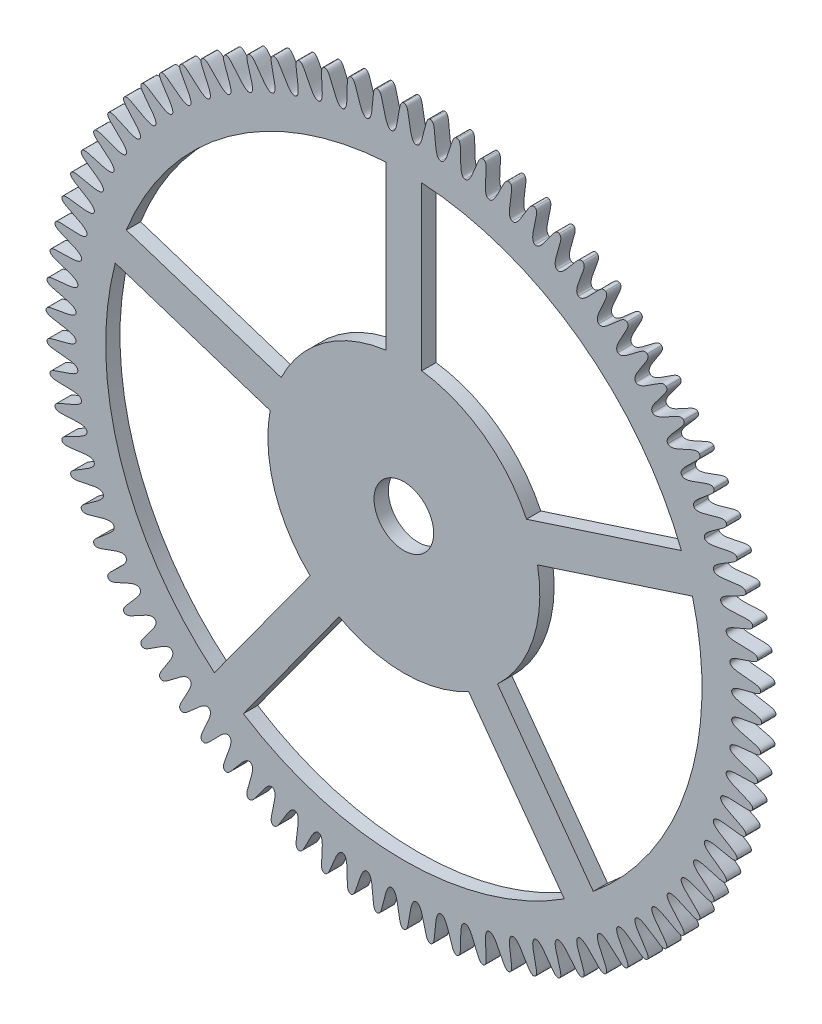
SolidWorks part; units mm, degrees
ref_plane "Alzado" through (0, 0, 0) normal (0, 0, 1) x (1, 0, 0)
ref_plane "Planta" through (0, 0, 0) normal (0, 1, 0) x (1, 0, 0)
ref_plane "Vista lateral" through (0, 0, 0) normal (1, 0, 0) x (0, 0, -1)
sketch "Sketch1" plane through (0, 0, 0) normal (0, 0, 1) x (1, 0, 0)
  line L0 (0, -5096.8663) -> (0, 249746.4475) construction
  line L1 (-5096.8663, 0) -> (249746.4475, 0) construction
  line L2 (0, 0) -> (1869.5597, 49965.0352) construction
  line L3 (0, 0) -> (-1869.5597, 49965.0352) construction
  circle A0 centre (0, 0) radius 6 construction
  circle A1 centre (0, 0) radius 5.5 construction
  circle A2 centre (0, 0) radius 5.75 construction
  spline S0 degree 3 poles (0, 6) (0.0624, 5.9999) (0.0733, 5.8707) (0.1163, 5.6176) (0.1469, 5.4976) (0.2057, 5.4979) knots 0 0 0 0 0.435079 0.535079 1 1 1 1
  spline S1 degree 3 poles (0, 6) (-0.0624, 5.9999) (-0.0733, 5.8707) (-0.1163, 5.6176) (-0.1469, 5.4976) (-0.2057, 5.4979) knots 0 0 0 0 0.435079 0.535079 1 1 1 1
  spline S2 degree 3 poles (0.4484, 5.9832) (0.3861, 5.9878) (0.3657, 5.8598) (0.3038, 5.6106) (0.2644, 5.4932) (0.2057, 5.4979) knots 0 0 0 0 0.435079 0.535079 1 1 1 1
  spline S3 degree 3 poles (0.4484, 5.9832) (0.5106, 5.9785) (0.5118, 5.8488) (0.5358, 5.5932) (0.5573, 5.4712) (0.616, 5.4672) knots 0 0 0 0 0.435079 0.535079 1 1 1 1
  spline S4 degree 3 poles (0.8943, 5.933) (0.8325, 5.9422) (0.8026, 5.8161) (0.7223, 5.5722) (0.6741, 5.4581) (0.616, 5.4672) knots 0 0 0 0 0.435079 0.535079 1 1 1 1
  spline S5 degree 3 poles (0.8943, 5.933) (0.956, 5.9236) (0.9474, 5.7942) (0.9522, 5.5375) (0.9646, 5.4143) (1.0228, 5.4059) knots 0 0 0 0 0.435079 0.535079 1 1 1 1
  spline S6 degree 3 poles (1.3351, 5.8496) (1.2743, 5.8634) (1.2349, 5.7398) (1.1367, 5.5026) (1.0801, 5.3924) (1.0228, 5.4059) knots 0 0 0 0 0.435079 0.535079 1 1 1 1
  spline S7 degree 3 poles (1.3351, 5.8496) (1.396, 5.8356) (1.3778, 5.7072) (1.3634, 5.4509) (1.3665, 5.3271) (1.424, 5.3143) knots 0 0 0 0 0.435079 0.535079 1 1 1 1
  spline S8 degree 3 poles (1.7685, 5.7334) (1.7089, 5.7518) (1.6604, 5.6315) (1.5447, 5.4023) (1.4801, 5.2966) (1.424, 5.3143) knots 0 0 0 0 0.435079 0.535079 1 1 1 1
  spline S9 degree 3 poles (1.7685, 5.7334) (1.8281, 5.715) (1.8004, 5.5883) (1.7669, 5.3337) (1.7608, 5.21) (1.8171, 5.193) knots 0 0 0 0 0.435079 0.535079 1 1 1 1
  spline S10 degree 3 poles (2.192, 5.5852) (2.1339, 5.608) (2.0766, 5.4917) (1.9441, 5.2717) (1.8718, 5.1712) (1.8171, 5.193) knots 0 0 0 0 0.435079 0.535079 1 1 1 1
  spline S11 degree 3 poles (2.192, 5.5852) (2.2501, 5.5624) (2.213, 5.4381) (2.1606, 5.1868) (2.1452, 5.0639) (2.2001, 5.0427) knots 0 0 0 0 0.435079 0.535079 1 1 1 1
  spline S12 degree 3 poles (2.6033, 5.4058) (2.5471, 5.4328) (2.4812, 5.3211) (2.3326, 5.1117) (2.253, 5.0169) (2.2001, 5.0427) knots 0 0 0 0 0.435079 0.535079 1 1 1 1
  spline S13 degree 3 poles (2.6033, 5.4058) (2.6595, 5.3787) (2.6132, 5.2575) (2.5421, 5.0108) (2.5176, 4.8894) (2.5708, 4.8642) knots 0 0 0 0 0.435079 0.535079 1 1 1 1
  spline S14 degree 3 poles (3, 5.1962) (2.9459, 5.2273) (2.8719, 5.1208) (2.7081, 4.9231) (2.6216, 4.8345) (2.5708, 4.8642) knots 0 0 0 0 0.435079 0.535079 1 1 1 1
  spline S15 degree 3 poles (3, 5.1962) (3.054, 5.1649) (2.9988, 5.0476) (2.9095, 4.8068) (2.876, 4.6876) (2.9271, 4.6585) knots 0 0 0 0 0.435079 0.535079 1 1 1 1
  spline S16 degree 3 poles (3.3799, 4.9574) (3.3283, 4.9925) (3.2466, 4.8919) (3.0684, 4.707) (2.9755, 4.625) (2.9271, 4.6585) knots 0 0 0 0 0.435079 0.535079 1 1 1 1
  spline S17 degree 3 poles (3.3799, 4.9574) (3.4315, 4.9222) (3.3676, 4.8093) (3.2606, 4.576) (3.2182, 4.4596) (3.2671, 4.4267) knots 0 0 0 0 0.435079 0.535079 1 1 1 1
  spline S18 degree 3 poles (3.7409, 4.691) (3.6921, 4.7299) (3.6031, 4.6356) (3.4116, 4.4645) (3.3129, 4.3897) (3.2671, 4.4267) knots 0 0 0 0 0.435079 0.535079 1 1 1 1
  spline S19 degree 3 poles (3.7409, 4.691) (3.7897, 4.652) (3.7176, 4.5442) (3.5934, 4.3195) (3.5425, 4.2066) (3.5887, 4.1702) knots 0 0 0 0 0.435079 0.535079 1 1 1 1
  spline S20 degree 3 poles (4.081, 4.3983) (4.0353, 4.4407) (3.9394, 4.3534) (3.7357, 4.1971) (3.6316, 4.1299) (3.5887, 4.1702) knots 0 0 0 0 0.435079 0.535079 1 1 1 1
  spline S21 degree 3 poles (4.081, 4.3983) (4.1267, 4.3558) (4.0468, 4.2537) (3.9062, 4.0389) (3.847, 3.9301) (3.8904, 3.8904) knots 0 0 0 0 0.435079 0.535079 1 1 1 1
  spline S22 degree 3 poles (4.3983, 4.081) (4.3558, 4.1267) (4.2537, 4.0468) (4.0389, 3.9062) (3.9301, 3.847) (3.8904, 3.8904) knots 0 0 0 0 0.435079 0.535079 1 1 1 1
  spline S23 degree 3 poles (4.3983, 4.081) (4.4407, 4.0353) (4.3534, 3.9394) (4.1971, 3.7357) (4.1299, 3.6316) (4.1702, 3.5887) knots 0 0 0 0 0.435079 0.535079 1 1 1 1
  spline S24 degree 3 poles (4.691, 3.7409) (4.652, 3.7897) (4.5442, 3.7176) (4.3195, 3.5934) (4.2066, 3.5425) (4.1702, 3.5887) knots 0 0 0 0 0.435079 0.535079 1 1 1 1
  spline S25 degree 3 poles (4.691, 3.7409) (4.7299, 3.6921) (4.6356, 3.6031) (4.4645, 3.4116) (4.3897, 3.3129) (4.4267, 3.2671) knots 0 0 0 0 0.435079 0.535079 1 1 1 1
  spline S26 degree 3 poles (4.9574, 3.3799) (4.9222, 3.4315) (4.8093, 3.3676) (4.576, 3.2606) (4.4596, 3.2182) (4.4267, 3.2671) knots 0 0 0 0 0.435079 0.535079 1 1 1 1
  spline S27 degree 3 poles (4.9574, 3.3799) (4.9925, 3.3283) (4.8919, 3.2466) (4.707, 3.0684) (4.625, 2.9755) (4.6585, 2.9271) knots 0 0 0 0 0.435079 0.535079 1 1 1 1
  spline S28 degree 3 poles (5.1962, 3) (5.1649, 3.054) (5.0476, 2.9988) (4.8068, 2.9095) (4.6876, 2.876) (4.6585, 2.9271) knots 0 0 0 0 0.435079 0.535079 1 1 1 1
  spline S29 degree 3 poles (5.1962, 3) (5.2273, 2.9459) (5.1208, 2.8719) (4.9231, 2.7081) (4.8345, 2.6216) (4.8642, 2.5708) knots 0 0 0 0 0.435079 0.535079 1 1 1 1
  spline S30 degree 3 poles (5.4058, 2.6033) (5.3787, 2.6595) (5.2575, 2.6132) (5.0108, 2.5421) (4.8894, 2.5176) (4.8642, 2.5708) knots 0 0 0 0 0.435079 0.535079 1 1 1 1
  spline S31 degree 3 poles (5.4058, 2.6033) (5.4328, 2.5471) (5.3211, 2.4812) (5.1117, 2.3326) (5.0169, 2.253) (5.0427, 2.2001) knots 0 0 0 0 0.435079 0.535079 1 1 1 1
  spline S32 degree 3 poles (5.5852, 2.192) (5.5624, 2.2501) (5.4381, 2.213) (5.1868, 2.1606) (5.0639, 2.1452) (5.0427, 2.2001) knots 0 0 0 0 0.435079 0.535079 1 1 1 1
  spline S33 degree 3 poles (5.5852, 2.192) (5.608, 2.1339) (5.4917, 2.0766) (5.2717, 1.9441) (5.1712, 1.8718) (5.193, 1.8171) knots 0 0 0 0 0.435079 0.535079 1 1 1 1
  spline S34 degree 3 poles (5.7334, 1.7685) (5.715, 1.8281) (5.5883, 1.8004) (5.3337, 1.7669) (5.21, 1.7608) (5.193, 1.8171) knots 0 0 0 0 0.435079 0.535079 1 1 1 1
  spline S35 degree 3 poles (5.7334, 1.7685) (5.7518, 1.7089) (5.6315, 1.6604) (5.4023, 1.5447) (5.2966, 1.4801) (5.3143, 1.424) knots 0 0 0 0 0.435079 0.535079 1 1 1 1
  spline S36 degree 3 poles (5.8496, 1.3351) (5.8356, 1.396) (5.7072, 1.3778) (5.4509, 1.3634) (5.3271, 1.3665) (5.3143, 1.424) knots 0 0 0 0 0.435079 0.535079 1 1 1 1
  spline S37 degree 3 poles (5.8496, 1.3351) (5.8634, 1.2743) (5.7398, 1.2349) (5.5026, 1.1367) (5.3924, 1.0801) (5.4059, 1.0228) knots 0 0 0 0 0.435079 0.535079 1 1 1 1
  spline S38 degree 3 poles (5.933, 0.8943) (5.9236, 0.956) (5.7942, 0.9474) (5.5375, 0.9522) (5.4143, 0.9646) (5.4059, 1.0228) knots 0 0 0 0 0.435079 0.535079 1 1 1 1
  spline S39 degree 3 poles (5.933, 0.8943) (5.9422, 0.8325) (5.8161, 0.8026) (5.5722, 0.7223) (5.4581, 0.6741) (5.4672, 0.616) knots 0 0 0 0 0.435079 0.535079 1 1 1 1
  spline S40 degree 3 poles (5.9832, 0.4484) (5.9785, 0.5106) (5.8488, 0.5118) (5.5932, 0.5358) (5.4712, 0.5573) (5.4672, 0.616) knots 0 0 0 0 0.435079 0.535079 1 1 1 1
  spline S41 degree 3 poles (5.9832, 0.4484) (5.9878, 0.3861) (5.8598, 0.3657) (5.6106, 0.3038) (5.4932, 0.2644) (5.4979, 0.2057) knots 0 0 0 0 0.435079 0.535079 1 1 1 1
  spline S42 degree 3 poles (6, 0) (5.9999, 0.0624) (5.8707, 0.0733) (5.6176, 0.1163) (5.4976, 0.1469) (5.4979, 0.2057) knots 0 0 0 0 0.435079 0.535079 1 1 1 1
  spline S43 degree 3 poles (6, 0) (5.9999, -0.0624) (5.8707, -0.0733) (5.6176, -0.1163) (5.4976, -0.1469) (5.4979, -0.2057) knots 0 0 0 0 0.435079 0.535079 1 1 1 1
  spline S44 degree 3 poles (5.9832, -0.4484) (5.9878, -0.3861) (5.8598, -0.3657) (5.6106, -0.3038) (5.4932, -0.2644) (5.4979, -0.2057) knots 0 0 0 0 0.435079 0.535079 1 1 1 1
  spline S45 degree 3 poles (5.9832, -0.4484) (5.9785, -0.5106) (5.8488, -0.5118) (5.5932, -0.5358) (5.4712, -0.5573) (5.4672, -0.616) knots 0 0 0 0 0.435079 0.535079 1 1 1 1
  spline S46 degree 3 poles (5.933, -0.8943) (5.9422, -0.8325) (5.8161, -0.8026) (5.5722, -0.7223) (5.4581, -0.6741) (5.4672, -0.616) knots 0 0 0 0 0.435079 0.535079 1 1 1 1
  spline S47 degree 3 poles (5.933, -0.8943) (5.9236, -0.956) (5.7942, -0.9474) (5.5375, -0.9522) (5.4143, -0.9646) (5.4059, -1.0228) knots 0 0 0 0 0.435079 0.535079 1 1 1 1
  spline S48 degree 3 poles (5.8496, -1.3351) (5.8634, -1.2743) (5.7398, -1.2349) (5.5026, -1.1367) (5.3924, -1.0801) (5.4059, -1.0228) knots 0 0 0 0 0.435079 0.535079 1 1 1 1
  spline S49 degree 3 poles (5.8496, -1.3351) (5.8356, -1.396) (5.7072, -1.3778) (5.4509, -1.3634) (5.3271, -1.3665) (5.3143, -1.424) knots 0 0 0 0 0.435079 0.535079 1 1 1 1
  spline S50 degree 3 poles (5.7334, -1.7685) (5.7518, -1.7089) (5.6315, -1.6604) (5.4023, -1.5447) (5.2966, -1.4801) (5.3143, -1.424) knots 0 0 0 0 0.435079 0.535079 1 1 1 1
  spline S51 degree 3 poles (5.7334, -1.7685) (5.715, -1.8281) (5.5883, -1.8004) (5.3337, -1.7669) (5.21, -1.7608) (5.193, -1.8171) knots 0 0 0 0 0.435079 0.535079 1 1 1 1
  spline S52 degree 3 poles (5.5852, -2.192) (5.608, -2.1339) (5.4917, -2.0766) (5.2717, -1.9441) (5.1712, -1.8718) (5.193, -1.8171) knots 0 0 0 0 0.435079 0.535079 1 1 1 1
  spline S53 degree 3 poles (5.5852, -2.192) (5.5624, -2.2501) (5.4381, -2.213) (5.1868, -2.1606) (5.0639, -2.1452) (5.0427, -2.2001) knots 0 0 0 0 0.435079 0.535079 1 1 1 1
  spline S54 degree 3 poles (5.4058, -2.6033) (5.4328, -2.5471) (5.3211, -2.4812) (5.1117, -2.3326) (5.0169, -2.253) (5.0427, -2.2001) knots 0 0 0 0 0.435079 0.535079 1 1 1 1
  spline S55 degree 3 poles (5.4058, -2.6033) (5.3787, -2.6595) (5.2575, -2.6132) (5.0108, -2.5421) (4.8894, -2.5176) (4.8642, -2.5708) knots 0 0 0 0 0.435079 0.535079 1 1 1 1
  spline S56 degree 3 poles (5.1962, -3) (5.2273, -2.9459) (5.1208, -2.8719) (4.9231, -2.7081) (4.8345, -2.6216) (4.8642, -2.5708) knots 0 0 0 0 0.435079 0.535079 1 1 1 1
  spline S57 degree 3 poles (5.1962, -3) (5.1649, -3.054) (5.0476, -2.9988) (4.8068, -2.9095) (4.6876, -2.876) (4.6585, -2.9271) knots 0 0 0 0 0.435079 0.535079 1 1 1 1
  spline S58 degree 3 poles (4.9574, -3.3799) (4.9925, -3.3283) (4.8919, -3.2466) (4.707, -3.0684) (4.625, -2.9755) (4.6585, -2.9271) knots 0 0 0 0 0.435079 0.535079 1 1 1 1
  spline S59 degree 3 poles (4.9574, -3.3799) (4.9222, -3.4315) (4.8093, -3.3676) (4.576, -3.2606) (4.4596, -3.2182) (4.4267, -3.2671) knots 0 0 0 0 0.435079 0.535079 1 1 1 1
  spline S60 degree 3 poles (4.691, -3.7409) (4.7299, -3.6921) (4.6356, -3.6031) (4.4645, -3.4116) (4.3897, -3.3129) (4.4267, -3.2671) knots 0 0 0 0 0.435079 0.535079 1 1 1 1
  spline S61 degree 3 poles (4.691, -3.7409) (4.652, -3.7897) (4.5442, -3.7176) (4.3195, -3.5934) (4.2066, -3.5425) (4.1702, -3.5887) knots 0 0 0 0 0.435079 0.535079 1 1 1 1
  spline S62 degree 3 poles (4.3983, -4.081) (4.4407, -4.0353) (4.3534, -3.9394) (4.1971, -3.7357) (4.1299, -3.6316) (4.1702, -3.5887) knots 0 0 0 0 0.435079 0.535079 1 1 1 1
  spline S63 degree 3 poles (4.3983, -4.081) (4.3558, -4.1267) (4.2537, -4.0468) (4.0389, -3.9062) (3.9301, -3.847) (3.8904, -3.8904) knots 0 0 0 0 0.435079 0.535079 1 1 1 1
  spline S64 degree 3 poles (4.081, -4.3983) (4.1267, -4.3558) (4.0468, -4.2537) (3.9062, -4.0389) (3.847, -3.9301) (3.8904, -3.8904) knots 0 0 0 0 0.435079 0.535079 1 1 1 1
  spline S65 degree 3 poles (4.081, -4.3983) (4.0353, -4.4407) (3.9394, -4.3534) (3.7357, -4.1971) (3.6316, -4.1299) (3.5887, -4.1702) knots 0 0 0 0 0.435079 0.535079 1 1 1 1
  spline S66 degree 3 poles (3.7409, -4.691) (3.7897, -4.652) (3.7176, -4.5442) (3.5934, -4.3195) (3.5425, -4.2066) (3.5887, -4.1702) knots 0 0 0 0 0.435079 0.535079 1 1 1 1
  spline S67 degree 3 poles (3.7409, -4.691) (3.6921, -4.7299) (3.6031, -4.6356) (3.4116, -4.4645) (3.3129, -4.3897) (3.2671, -4.4267) knots 0 0 0 0 0.435079 0.535079 1 1 1 1
  spline S68 degree 3 poles (3.3799, -4.9574) (3.4315, -4.9222) (3.3676, -4.8093) (3.2606, -4.576) (3.2182, -4.4596) (3.2671, -4.4267) knots 0 0 0 0 0.435079 0.535079 1 1 1 1
  spline S69 degree 3 poles (3.3799, -4.9574) (3.3283, -4.9925) (3.2466, -4.8919) (3.0684, -4.707) (2.9755, -4.625) (2.9271, -4.6585) knots 0 0 0 0 0.435079 0.535079 1 1 1 1
  spline S70 degree 3 poles (3, -5.1962) (3.054, -5.1649) (2.9988, -5.0476) (2.9095, -4.8068) (2.876, -4.6876) (2.9271, -4.6585) knots 0 0 0 0 0.435079 0.535079 1 1 1 1
  spline S71 degree 3 poles (3, -5.1962) (2.9459, -5.2273) (2.8719, -5.1208) (2.7081, -4.9231) (2.6216, -4.8345) (2.5708, -4.8642) knots 0 0 0 0 0.435079 0.535079 1 1 1 1
  spline S72 degree 3 poles (2.6033, -5.4058) (2.6595, -5.3787) (2.6132, -5.2575) (2.5421, -5.0108) (2.5176, -4.8894) (2.5708, -4.8642) knots 0 0 0 0 0.435079 0.535079 1 1 1 1
  spline S73 degree 3 poles (2.6033, -5.4058) (2.5471, -5.4328) (2.4812, -5.3211) (2.3326, -5.1117) (2.253, -5.0169) (2.2001, -5.0427) knots 0 0 0 0 0.435079 0.535079 1 1 1 1
  spline S74 degree 3 poles (2.192, -5.5852) (2.2501, -5.5624) (2.213, -5.4381) (2.1606, -5.1868) (2.1452, -5.0639) (2.2001, -5.0427) knots 0 0 0 0 0.435079 0.535079 1 1 1 1
  spline S75 degree 3 poles (2.192, -5.5852) (2.1339, -5.608) (2.0766, -5.4917) (1.9441, -5.2717) (1.8718, -5.1712) (1.8171, -5.193) knots 0 0 0 0 0.435079 0.535079 1 1 1 1
  spline S76 degree 3 poles (1.7685, -5.7334) (1.8281, -5.715) (1.8004, -5.5883) (1.7669, -5.3337) (1.7608, -5.21) (1.8171, -5.193) knots 0 0 0 0 0.435079 0.535079 1 1 1 1
  spline S77 degree 3 poles (1.7685, -5.7334) (1.7089, -5.7518) (1.6604, -5.6315) (1.5447, -5.4023) (1.4801, -5.2966) (1.424, -5.3143) knots 0 0 0 0 0.435079 0.535079 1 1 1 1
  spline S78 degree 3 poles (1.3351, -5.8496) (1.396, -5.8356) (1.3778, -5.7072) (1.3634, -5.4509) (1.3665, -5.3271) (1.424, -5.3143) knots 0 0 0 0 0.435079 0.535079 1 1 1 1
  spline S79 degree 3 poles (1.3351, -5.8496) (1.2743, -5.8634) (1.2349, -5.7398) (1.1367, -5.5026) (1.0801, -5.3924) (1.0228, -5.4059) knots 0 0 0 0 0.435079 0.535079 1 1 1 1
  spline S80 degree 3 poles (0.8943, -5.933) (0.956, -5.9236) (0.9474, -5.7942) (0.9522, -5.5375) (0.9646, -5.4143) (1.0228, -5.4059) knots 0 0 0 0 0.435079 0.535079 1 1 1 1
  spline S81 degree 3 poles (0.8943, -5.933) (0.8325, -5.9422) (0.8026, -5.8161) (0.7223, -5.5722) (0.6741, -5.4581) (0.616, -5.4672) knots 0 0 0 0 0.435079 0.535079 1 1 1 1
  spline S82 degree 3 poles (0.4484, -5.9832) (0.5106, -5.9785) (0.5118, -5.8488) (0.5358, -5.5932) (0.5573, -5.4712) (0.616, -5.4672) knots 0 0 0 0 0.435079 0.535079 1 1 1 1
  spline S83 degree 3 poles (0.4484, -5.9832) (0.3861, -5.9878) (0.3657, -5.8598) (0.3038, -5.6106) (0.2644, -5.4932) (0.2057, -5.4979) knots 0 0 0 0 0.435079 0.535079 1 1 1 1
  spline S84 degree 3 poles (0, -6) (0.0624, -5.9999) (0.0733, -5.8707) (0.1163, -5.6176) (0.1469, -5.4976) (0.2057, -5.4979) knots 0 0 0 0 0.435079 0.535079 1 1 1 1
  spline S85 degree 3 poles (0, -6) (-0.0624, -5.9999) (-0.0733, -5.8707) (-0.1163, -5.6176) (-0.1469, -5.4976) (-0.2057, -5.4979) knots 0 0 0 0 0.435079 0.535079 1 1 1 1
  spline S86 degree 3 poles (-0.4484, -5.9832) (-0.3861, -5.9878) (-0.3657, -5.8598) (-0.3038, -5.6106) (-0.2644, -5.4932) (-0.2057, -5.4979) knots 0 0 0 0 0.435079 0.535079 1 1 1 1
  spline S87 degree 3 poles (-0.4484, -5.9832) (-0.5106, -5.9785) (-0.5118, -5.8488) (-0.5358, -5.5932) (-0.5573, -5.4712) (-0.616, -5.4672) knots 0 0 0 0 0.435079 0.535079 1 1 1 1
  spline S88 degree 3 poles (-0.8943, -5.933) (-0.8325, -5.9422) (-0.8026, -5.8161) (-0.7223, -5.5722) (-0.6741, -5.4581) (-0.616, -5.4672) knots 0 0 0 0 0.435079 0.535079 1 1 1 1
  spline S89 degree 3 poles (-0.8943, -5.933) (-0.956, -5.9236) (-0.9474, -5.7942) (-0.9522, -5.5375) (-0.9646, -5.4143) (-1.0228, -5.4059) knots 0 0 0 0 0.435079 0.535079 1 1 1 1
  spline S90 degree 3 poles (-1.3351, -5.8496) (-1.2743, -5.8634) (-1.2349, -5.7398) (-1.1367, -5.5026) (-1.0801, -5.3924) (-1.0228, -5.4059) knots 0 0 0 0 0.435079 0.535079 1 1 1 1
  spline S91 degree 3 poles (-1.3351, -5.8496) (-1.396, -5.8356) (-1.3778, -5.7072) (-1.3634, -5.4509) (-1.3665, -5.3271) (-1.424, -5.3143) knots 0 0 0 0 0.435079 0.535079 1 1 1 1
  spline S92 degree 3 poles (-1.7685, -5.7334) (-1.7089, -5.7518) (-1.6604, -5.6315) (-1.5447, -5.4023) (-1.4801, -5.2966) (-1.424, -5.3143) knots 0 0 0 0 0.435079 0.535079 1 1 1 1
  spline S93 degree 3 poles (-1.7685, -5.7334) (-1.8281, -5.715) (-1.8004, -5.5883) (-1.7669, -5.3337) (-1.7608, -5.21) (-1.8171, -5.193) knots 0 0 0 0 0.435079 0.535079 1 1 1 1
  spline S94 degree 3 poles (-2.192, -5.5852) (-2.1339, -5.608) (-2.0766, -5.4917) (-1.9441, -5.2717) (-1.8718, -5.1712) (-1.8171, -5.193) knots 0 0 0 0 0.435079 0.535079 1 1 1 1
  spline S95 degree 3 poles (-2.192, -5.5852) (-2.2501, -5.5624) (-2.213, -5.4381) (-2.1606, -5.1868) (-2.1452, -5.0639) (-2.2001, -5.0427) knots 0 0 0 0 0.435079 0.535079 1 1 1 1
  spline S96 degree 3 poles (-2.6033, -5.4058) (-2.5471, -5.4328) (-2.4812, -5.3211) (-2.3326, -5.1117) (-2.253, -5.0169) (-2.2001, -5.0427) knots 0 0 0 0 0.435079 0.535079 1 1 1 1
  spline S97 degree 3 poles (-2.6033, -5.4058) (-2.6595, -5.3787) (-2.6132, -5.2575) (-2.5421, -5.0108) (-2.5176, -4.8894) (-2.5708, -4.8642) knots 0 0 0 0 0.435079 0.535079 1 1 1 1
  spline S98 degree 3 poles (-3, -5.1962) (-2.9459, -5.2273) (-2.8719, -5.1208) (-2.7081, -4.9231) (-2.6216, -4.8345) (-2.5708, -4.8642) knots 0 0 0 0 0.435079 0.535079 1 1 1 1
  spline S99 degree 3 poles (-3, -5.1962) (-3.054, -5.1649) (-2.9988, -5.0476) (-2.9095, -4.8068) (-2.876, -4.6876) (-2.9271, -4.6585) knots 0 0 0 0 0.435079 0.535079 1 1 1 1
  spline S100 degree 3 poles (-3.3799, -4.9574) (-3.3283, -4.9925) (-3.2466, -4.8919) (-3.0684, -4.707) (-2.9755, -4.625) (-2.9271, -4.6585) knots 0 0 0 0 0.435079 0.535079 1 1 1 1
  spline S101 degree 3 poles (-3.3799, -4.9574) (-3.4315, -4.9222) (-3.3676, -4.8093) (-3.2606, -4.576) (-3.2182, -4.4596) (-3.2671, -4.4267) knots 0 0 0 0 0.435079 0.535079 1 1 1 1
  spline S102 degree 3 poles (-3.7409, -4.691) (-3.6921, -4.7299) (-3.6031, -4.6356) (-3.4116, -4.4645) (-3.3129, -4.3897) (-3.2671, -4.4267) knots 0 0 0 0 0.435079 0.535079 1 1 1 1
  spline S103 degree 3 poles (-3.7409, -4.691) (-3.7897, -4.652) (-3.7176, -4.5442) (-3.5934, -4.3195) (-3.5425, -4.2066) (-3.5887, -4.1702) knots 0 0 0 0 0.435079 0.535079 1 1 1 1
  spline S104 degree 3 poles (-4.081, -4.3983) (-4.0353, -4.4407) (-3.9394, -4.3534) (-3.7357, -4.1971) (-3.6316, -4.1299) (-3.5887, -4.1702) knots 0 0 0 0 0.435079 0.535079 1 1 1 1
  spline S105 degree 3 poles (-4.081, -4.3983) (-4.1267, -4.3558) (-4.0468, -4.2537) (-3.9062, -4.0389) (-3.847, -3.9301) (-3.8904, -3.8904) knots 0 0 0 0 0.435079 0.535079 1 1 1 1
  spline S106 degree 3 poles (-4.3983, -4.081) (-4.3558, -4.1267) (-4.2537, -4.0468) (-4.0389, -3.9062) (-3.9301, -3.847) (-3.8904, -3.8904) knots 0 0 0 0 0.435079 0.535079 1 1 1 1
  spline S107 degree 3 poles (-4.3983, -4.081) (-4.4407, -4.0353) (-4.3534, -3.9394) (-4.1971, -3.7357) (-4.1299, -3.6316) (-4.1702, -3.5887) knots 0 0 0 0 0.435079 0.535079 1 1 1 1
  spline S108 degree 3 poles (-4.691, -3.7409) (-4.652, -3.7897) (-4.5442, -3.7176) (-4.3195, -3.5934) (-4.2066, -3.5425) (-4.1702, -3.5887) knots 0 0 0 0 0.435079 0.535079 1 1 1 1
  spline S109 degree 3 poles (-4.691, -3.7409) (-4.7299, -3.6921) (-4.6356, -3.6031) (-4.4645, -3.4116) (-4.3897, -3.3129) (-4.4267, -3.2671) knots 0 0 0 0 0.435079 0.535079 1 1 1 1
  spline S110 degree 3 poles (-4.9574, -3.3799) (-4.9222, -3.4315) (-4.8093, -3.3676) (-4.576, -3.2606) (-4.4596, -3.2182) (-4.4267, -3.2671) knots 0 0 0 0 0.435079 0.535079 1 1 1 1
  spline S111 degree 3 poles (-4.9574, -3.3799) (-4.9925, -3.3283) (-4.8919, -3.2466) (-4.707, -3.0684) (-4.625, -2.9755) (-4.6585, -2.9271) knots 0 0 0 0 0.435079 0.535079 1 1 1 1
  spline S112 degree 3 poles (-5.1962, -3) (-5.1649, -3.054) (-5.0476, -2.9988) (-4.8068, -2.9095) (-4.6876, -2.876) (-4.6585, -2.9271) knots 0 0 0 0 0.435079 0.535079 1 1 1 1
  spline S113 degree 3 poles (-5.1962, -3) (-5.2273, -2.9459) (-5.1208, -2.8719) (-4.9231, -2.7081) (-4.8345, -2.6216) (-4.8642, -2.5708) knots 0 0 0 0 0.435079 0.535079 1 1 1 1
  spline S114 degree 3 poles (-5.4058, -2.6033) (-5.3787, -2.6595) (-5.2575, -2.6132) (-5.0108, -2.5421) (-4.8894, -2.5176) (-4.8642, -2.5708) knots 0 0 0 0 0.435079 0.535079 1 1 1 1
  spline S115 degree 3 poles (-5.4058, -2.6033) (-5.4328, -2.5471) (-5.3211, -2.4812) (-5.1117, -2.3326) (-5.0169, -2.253) (-5.0427, -2.2001) knots 0 0 0 0 0.435079 0.535079 1 1 1 1
  spline S116 degree 3 poles (-5.5852, -2.192) (-5.5624, -2.2501) (-5.4381, -2.213) (-5.1868, -2.1606) (-5.0639, -2.1452) (-5.0427, -2.2001) knots 0 0 0 0 0.435079 0.535079 1 1 1 1
  spline S117 degree 3 poles (-5.5852, -2.192) (-5.608, -2.1339) (-5.4917, -2.0766) (-5.2717, -1.9441) (-5.1712, -1.8718) (-5.193, -1.8171) knots 0 0 0 0 0.435079 0.535079 1 1 1 1
  spline S118 degree 3 poles (-5.7334, -1.7685) (-5.715, -1.8281) (-5.5883, -1.8004) (-5.3337, -1.7669) (-5.21, -1.7608) (-5.193, -1.8171) knots 0 0 0 0 0.435079 0.535079 1 1 1 1
  spline S119 degree 3 poles (-5.7334, -1.7685) (-5.7518, -1.7089) (-5.6315, -1.6604) (-5.4023, -1.5447) (-5.2966, -1.4801) (-5.3143, -1.424) knots 0 0 0 0 0.435079 0.535079 1 1 1 1
  spline S120 degree 3 poles (-5.8496, -1.3351) (-5.8356, -1.396) (-5.7072, -1.3778) (-5.4509, -1.3634) (-5.3271, -1.3665) (-5.3143, -1.424) knots 0 0 0 0 0.435079 0.535079 1 1 1 1
  spline S121 degree 3 poles (-5.8496, -1.3351) (-5.8634, -1.2743) (-5.7398, -1.2349) (-5.5026, -1.1367) (-5.3924, -1.0801) (-5.4059, -1.0228) knots 0 0 0 0 0.435079 0.535079 1 1 1 1
  spline S122 degree 3 poles (-5.933, -0.8943) (-5.9236, -0.956) (-5.7942, -0.9474) (-5.5375, -0.9522) (-5.4143, -0.9646) (-5.4059, -1.0228) knots 0 0 0 0 0.435079 0.535079 1 1 1 1
  spline S123 degree 3 poles (-5.933, -0.8943) (-5.9422, -0.8325) (-5.8161, -0.8026) (-5.5722, -0.7223) (-5.4581, -0.6741) (-5.4672, -0.616) knots 0 0 0 0 0.435079 0.535079 1 1 1 1
  spline S124 degree 3 poles (-5.9832, -0.4484) (-5.9785, -0.5106) (-5.8488, -0.5118) (-5.5932, -0.5358) (-5.4712, -0.5573) (-5.4672, -0.616) knots 0 0 0 0 0.435079 0.535079 1 1 1 1
  spline S125 degree 3 poles (-5.9832, -0.4484) (-5.9878, -0.3861) (-5.8598, -0.3657) (-5.6106, -0.3038) (-5.4932, -0.2644) (-5.4979, -0.2057) knots 0 0 0 0 0.435079 0.535079 1 1 1 1
  spline S126 degree 3 poles (-6, 0) (-5.9999, -0.0624) (-5.8707, -0.0733) (-5.6176, -0.1163) (-5.4976, -0.1469) (-5.4979, -0.2057) knots 0 0 0 0 0.435079 0.535079 1 1 1 1
  spline S127 degree 3 poles (-6, 0) (-5.9999, 0.0624) (-5.8707, 0.0733) (-5.6176, 0.1163) (-5.4976, 0.1469) (-5.4979, 0.2057) knots 0 0 0 0 0.435079 0.535079 1 1 1 1
  spline S128 degree 3 poles (-5.9832, 0.4484) (-5.9878, 0.3861) (-5.8598, 0.3657) (-5.6106, 0.3038) (-5.4932, 0.2644) (-5.4979, 0.2057) knots 0 0 0 0 0.435079 0.535079 1 1 1 1
  spline S129 degree 3 poles (-5.9832, 0.4484) (-5.9785, 0.5106) (-5.8488, 0.5118) (-5.5932, 0.5358) (-5.4712, 0.5573) (-5.4672, 0.616) knots 0 0 0 0 0.435079 0.535079 1 1 1 1
  spline S130 degree 3 poles (-5.933, 0.8943) (-5.9422, 0.8325) (-5.8161, 0.8026) (-5.5722, 0.7223) (-5.4581, 0.6741) (-5.4672, 0.616) knots 0 0 0 0 0.435079 0.535079 1 1 1 1
  spline S131 degree 3 poles (-5.933, 0.8943) (-5.9236, 0.956) (-5.7942, 0.9474) (-5.5375, 0.9522) (-5.4143, 0.9646) (-5.4059, 1.0228) knots 0 0 0 0 0.435079 0.535079 1 1 1 1
  spline S132 degree 3 poles (-5.8496, 1.3351) (-5.8634, 1.2743) (-5.7398, 1.2349) (-5.5026, 1.1367) (-5.3924, 1.0801) (-5.4059, 1.0228) knots 0 0 0 0 0.435079 0.535079 1 1 1 1
  spline S133 degree 3 poles (-5.8496, 1.3351) (-5.8356, 1.396) (-5.7072, 1.3778) (-5.4509, 1.3634) (-5.3271, 1.3665) (-5.3143, 1.424) knots 0 0 0 0 0.435079 0.535079 1 1 1 1
  spline S134 degree 3 poles (-5.7334, 1.7685) (-5.7518, 1.7089) (-5.6315, 1.6604) (-5.4023, 1.5447) (-5.2966, 1.4801) (-5.3143, 1.424) knots 0 0 0 0 0.435079 0.535079 1 1 1 1
  spline S135 degree 3 poles (-5.7334, 1.7685) (-5.715, 1.8281) (-5.5883, 1.8004) (-5.3337, 1.7669) (-5.21, 1.7608) (-5.193, 1.8171) knots 0 0 0 0 0.435079 0.535079 1 1 1 1
  spline S136 degree 3 poles (-5.5852, 2.192) (-5.608, 2.1339) (-5.4917, 2.0766) (-5.2717, 1.9441) (-5.1712, 1.8718) (-5.193, 1.8171) knots 0 0 0 0 0.435079 0.535079 1 1 1 1
  spline S137 degree 3 poles (-5.5852, 2.192) (-5.5624, 2.2501) (-5.4381, 2.213) (-5.1868, 2.1606) (-5.0639, 2.1452) (-5.0427, 2.2001) knots 0 0 0 0 0.435079 0.535079 1 1 1 1
  spline S138 degree 3 poles (-5.4058, 2.6033) (-5.4328, 2.5471) (-5.3211, 2.4812) (-5.1117, 2.3326) (-5.0169, 2.253) (-5.0427, 2.2001) knots 0 0 0 0 0.435079 0.535079 1 1 1 1
  spline S139 degree 3 poles (-5.4058, 2.6033) (-5.3787, 2.6595) (-5.2575, 2.6132) (-5.0108, 2.5421) (-4.8894, 2.5176) (-4.8642, 2.5708) knots 0 0 0 0 0.435079 0.535079 1 1 1 1
  spline S140 degree 3 poles (-5.1962, 3) (-5.2273, 2.9459) (-5.1208, 2.8719) (-4.9231, 2.7081) (-4.8345, 2.6216) (-4.8642, 2.5708) knots 0 0 0 0 0.435079 0.535079 1 1 1 1
  spline S141 degree 3 poles (-5.1962, 3) (-5.1649, 3.054) (-5.0476, 2.9988) (-4.8068, 2.9095) (-4.6876, 2.876) (-4.6585, 2.9271) knots 0 0 0 0 0.435079 0.535079 1 1 1 1
  spline S142 degree 3 poles (-4.9574, 3.3799) (-4.9925, 3.3283) (-4.8919, 3.2466) (-4.707, 3.0684) (-4.625, 2.9755) (-4.6585, 2.9271) knots 0 0 0 0 0.435079 0.535079 1 1 1 1
  spline S143 degree 3 poles (-4.9574, 3.3799) (-4.9222, 3.4315) (-4.8093, 3.3676) (-4.576, 3.2606) (-4.4596, 3.2182) (-4.4267, 3.2671) knots 0 0 0 0 0.435079 0.535079 1 1 1 1
  spline S144 degree 3 poles (-4.691, 3.7409) (-4.7299, 3.6921) (-4.6356, 3.6031) (-4.4645, 3.4116) (-4.3897, 3.3129) (-4.4267, 3.2671) knots 0 0 0 0 0.435079 0.535079 1 1 1 1
  spline S145 degree 3 poles (-4.691, 3.7409) (-4.652, 3.7897) (-4.5442, 3.7176) (-4.3195, 3.5934) (-4.2066, 3.5425) (-4.1702, 3.5887) knots 0 0 0 0 0.435079 0.535079 1 1 1 1
  spline S146 degree 3 poles (-4.3983, 4.081) (-4.4407, 4.0353) (-4.3534, 3.9394) (-4.1971, 3.7357) (-4.1299, 3.6316) (-4.1702, 3.5887) knots 0 0 0 0 0.435079 0.535079 1 1 1 1
  spline S147 degree 3 poles (-4.3983, 4.081) (-4.3558, 4.1267) (-4.2537, 4.0468) (-4.0389, 3.9062) (-3.9301, 3.847) (-3.8904, 3.8904) knots 0 0 0 0 0.435079 0.535079 1 1 1 1
  spline S148 degree 3 poles (-4.081, 4.3983) (-4.1267, 4.3558) (-4.0468, 4.2537) (-3.9062, 4.0389) (-3.847, 3.9301) (-3.8904, 3.8904) knots 0 0 0 0 0.435079 0.535079 1 1 1 1
  spline S149 degree 3 poles (-4.081, 4.3983) (-4.0353, 4.4407) (-3.9394, 4.3534) (-3.7357, 4.1971) (-3.6316, 4.1299) (-3.5887, 4.1702) knots 0 0 0 0 0.435079 0.535079 1 1 1 1
  spline S150 degree 3 poles (-3.7409, 4.691) (-3.7897, 4.652) (-3.7176, 4.5442) (-3.5934, 4.3195) (-3.5425, 4.2066) (-3.5887, 4.1702) knots 0 0 0 0 0.435079 0.535079 1 1 1 1
  spline S151 degree 3 poles (-3.7409, 4.691) (-3.6921, 4.7299) (-3.6031, 4.6356) (-3.4116, 4.4645) (-3.3129, 4.3897) (-3.2671, 4.4267) knots 0 0 0 0 0.435079 0.535079 1 1 1 1
  spline S152 degree 3 poles (-3.3799, 4.9574) (-3.4315, 4.9222) (-3.3676, 4.8093) (-3.2606, 4.576) (-3.2182, 4.4596) (-3.2671, 4.4267) knots 0 0 0 0 0.435079 0.535079 1 1 1 1
  spline S153 degree 3 poles (-3.3799, 4.9574) (-3.3283, 4.9925) (-3.2466, 4.8919) (-3.0684, 4.707) (-2.9755, 4.625) (-2.9271, 4.6585) knots 0 0 0 0 0.435079 0.535079 1 1 1 1
  spline S154 degree 3 poles (-3, 5.1962) (-3.054, 5.1649) (-2.9988, 5.0476) (-2.9095, 4.8068) (-2.876, 4.6876) (-2.9271, 4.6585) knots 0 0 0 0 0.435079 0.535079 1 1 1 1
  spline S155 degree 3 poles (-3, 5.1962) (-2.9459, 5.2273) (-2.8719, 5.1208) (-2.7081, 4.9231) (-2.6216, 4.8345) (-2.5708, 4.8642) knots 0 0 0 0 0.435079 0.535079 1 1 1 1
  spline S156 degree 3 poles (-2.6033, 5.4058) (-2.6595, 5.3787) (-2.6132, 5.2575) (-2.5421, 5.0108) (-2.5176, 4.8894) (-2.5708, 4.8642) knots 0 0 0 0 0.435079 0.535079 1 1 1 1
  spline S157 degree 3 poles (-2.6033, 5.4058) (-2.5471, 5.4328) (-2.4812, 5.3211) (-2.3326, 5.1117) (-2.253, 5.0169) (-2.2001, 5.0427) knots 0 0 0 0 0.435079 0.535079 1 1 1 1
  spline S158 degree 3 poles (-2.192, 5.5852) (-2.2501, 5.5624) (-2.213, 5.4381) (-2.1606, 5.1868) (-2.1452, 5.0639) (-2.2001, 5.0427) knots 0 0 0 0 0.435079 0.535079 1 1 1 1
  spline S159 degree 3 poles (-2.192, 5.5852) (-2.1339, 5.608) (-2.0766, 5.4917) (-1.9441, 5.2717) (-1.8718, 5.1712) (-1.8171, 5.193) knots 0 0 0 0 0.435079 0.535079 1 1 1 1
  spline S160 degree 3 poles (-1.7685, 5.7334) (-1.8281, 5.715) (-1.8004, 5.5883) (-1.7669, 5.3337) (-1.7608, 5.21) (-1.8171, 5.193) knots 0 0 0 0 0.435079 0.535079 1 1 1 1
  spline S161 degree 3 poles (-1.7685, 5.7334) (-1.7089, 5.7518) (-1.6604, 5.6315) (-1.5447, 5.4023) (-1.4801, 5.2966) (-1.424, 5.3143) knots 0 0 0 0 0.435079 0.535079 1 1 1 1
  spline S162 degree 3 poles (-1.3351, 5.8496) (-1.396, 5.8356) (-1.3778, 5.7072) (-1.3634, 5.4509) (-1.3665, 5.3271) (-1.424, 5.3143) knots 0 0 0 0 0.435079 0.535079 1 1 1 1
  spline S163 degree 3 poles (-1.3351, 5.8496) (-1.2743, 5.8634) (-1.2349, 5.7398) (-1.1367, 5.5026) (-1.0801, 5.3924) (-1.0228, 5.4059) knots 0 0 0 0 0.435079 0.535079 1 1 1 1
  spline S164 degree 3 poles (-0.8943, 5.933) (-0.956, 5.9236) (-0.9474, 5.7942) (-0.9522, 5.5375) (-0.9646, 5.4143) (-1.0228, 5.4059) knots 0 0 0 0 0.435079 0.535079 1 1 1 1
  spline S165 degree 3 poles (-0.8943, 5.933) (-0.8325, 5.9422) (-0.8026, 5.8161) (-0.7223, 5.5722) (-0.6741, 5.4581) (-0.616, 5.4672) knots 0 0 0 0 0.435079 0.535079 1 1 1 1
  spline S166 degree 3 poles (-0.4484, 5.9832) (-0.5106, 5.9785) (-0.5118, 5.8488) (-0.5358, 5.5932) (-0.5573, 5.4712) (-0.616, 5.4672) knots 0 0 0 0 0.435079 0.535079 1 1 1 1
  spline S167 degree 3 poles (-0.4484, 5.9832) (-0.3861, 5.9878) (-0.3657, 5.8598) (-0.3038, 5.6106) (-0.2644, 5.4932) (-0.2057, 5.4979) knots 0 0 0 0 0.435079 0.535079 1 1 1 1
  point P8 (0, 6)
  point P12 (0.2057, 5.4979)
  point P13 (-0.2057, 5.4962)
  point P439 (0, 0)
  dimension "D1" = 12
  dimension "D2" = 11
  dimension "D3" = 2.143
  dimension "D5" = 11.5
  dimension "D4" = 2.143
extrude "Boss-Extrude1 (84 teeth)" add sketch "Sketch1" along normal blind 0.24
sketch "Sketch2" plane through (0, 0, 0) normal (0, 0, 1) x (1, 0, 0)
  line L0 (0, -1000) -> (0, 49000) construction
  line L1 (0.3, -999.9548) -> (0.3, 49000.0452) construction
  line L2 (-0.3, -999.776) -> (-0.3, 49000.224) construction
  line L3 (-0.3, 4.991) -> (-0.3, 2.2602)
  line L4 (0.3, 4.991) -> (0.3, 2.2602)
  line L5 (4.8394, 1.257) -> (2.2423, 0.4131)
  line L6 (4.654, 1.8276) -> (2.0569, 0.9838)
  line L7 (2.6909, -4.2141) -> (1.0858, -2.0049)
  line L8 (3.1763, -3.8615) -> (1.5712, -1.6522)
  line L9 (-3.1763, -3.8615) -> (-1.5712, -1.6522)
  line L10 (-2.6909, -4.2141) -> (-1.0858, -2.0049)
  line L11 (-4.654, 1.8276) -> (-2.0569, 0.9838)
  line L12 (-4.8394, 1.257) -> (-2.2423, 0.4131)
  arc A0 (-0.3, 4.991) -> (-4.654, 1.8276) centre (0, 0) ccw
  arc A1 (-0.3, 2.2602) -> (-2.0569, 0.9838) centre (0, 0) ccw
  arc A2 (-4.8394, 1.257) -> (-3.1763, -3.8615) centre (0, 0) ccw
  arc A3 (-2.2423, 0.4131) -> (-1.5712, -1.6522) centre (0, 0) ccw
  arc A4 (2.0569, 0.9838) -> (0.3, 2.2602) centre (0, 0) ccw
  arc A5 (4.654, 1.8276) -> (0.3, 4.991) centre (0, 0) ccw
  arc A6 (3.1763, -3.8615) -> (4.8394, 1.257) centre (0, 0) ccw
  arc A7 (1.5712, -1.6522) -> (2.2423, 0.4131) centre (0, 0) ccw
  arc A8 (-1.0858, -2.0049) -> (1.0858, -2.0049) centre (0, 0) ccw
  arc A9 (-2.6909, -4.2141) -> (2.6909, -4.2141) centre (0, 0) ccw
  circle A10 centre (0, 0) radius 0.5
  point P31 (0, 0)
  dimension "D1" = 10
  dimension "D2" = 4.56
  dimension "D6" = 1
  dimension "D3" = 0.3
  dimension "D4" = 0.3
  dimension "D5" = 5
extrude "Cut-Extrude1" cut sketch "Sketch2" along normal up to next
